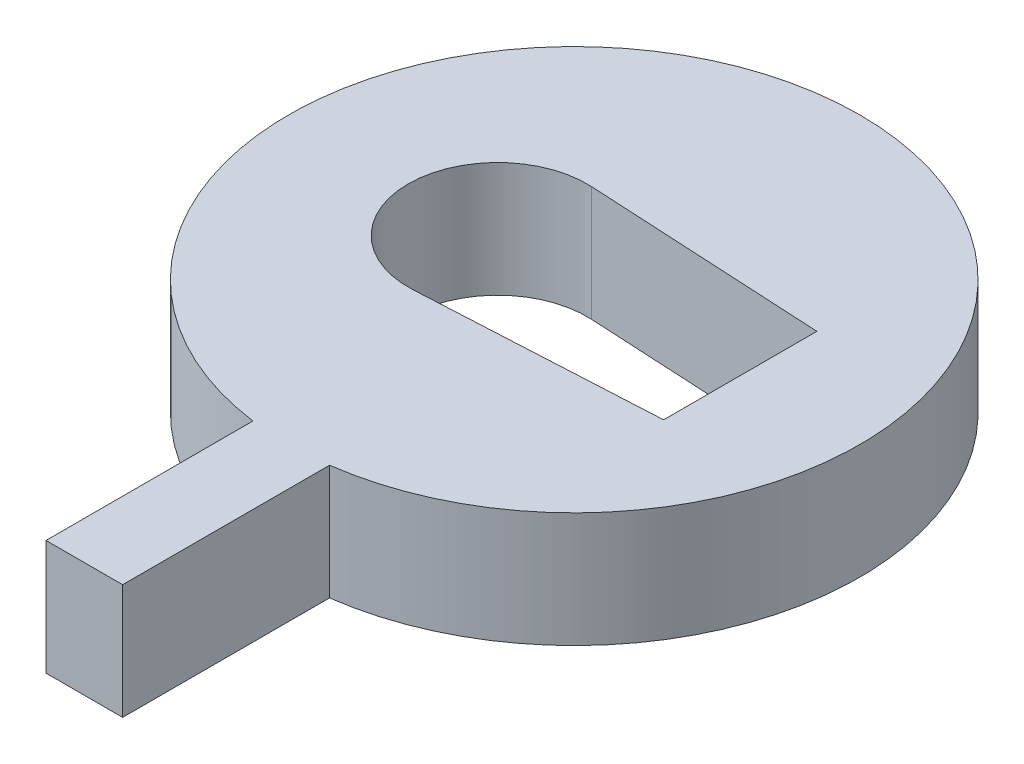
SolidWorks part; units mm, degrees
ref_plane "前视基准面" through (0, 0, 0) normal (0, 0, 1) x (1, 0, 0)
ref_plane "上视基准面" through (0, 0, 0) normal (0, 1, 0) x (1, 0, 0)
ref_plane "右视基准面" through (0, 0, 0) normal (1, 0, 0) x (0, 0, -1)
other "Configuration Table"
sketch "草图1" plane through (0, 0, 0) normal (0, 1, 0) x (1, 0, 0)
  line L1 (10, -5) -> (-10, -5)
  line L2 (10, -5) -> (10, 5)
  line L3 (10, 5) -> (-10, 5)
  line L4 (-10, -5) -> (-10, 5)
  line L5 (10, -5) -> (-10, 5) construction
  line L6 (10, 5) -> (-10, -5) construction
  point P0 (0, 0)
  dimension "D1" = 20
  dimension "D2" = 10
extrude "凸台-拉伸1" add sketch "草图1" along normal blind 4.5
sketch "草图2" plane through (0, 4.5, 0) normal (0, 1, 0) x (1, 0, 0)
  line L0 (-2.8142, 3.4951) -> (6.5, 3)
  line L1 (6.5, 3) -> (6.5, -3)
  line L2 (6.5, -3) -> (-2.8142, -3.4951)
  line L3 (0, 5) -> (0, -5) construction
  line L4 (-6.5, 0) -> (6.5, 0) construction
  line L5 (10, 5) -> (-10, 5) construction
  line L6 (-10, -5) -> (10, -5) construction
  arc A1 (-2.8142, 3.4951) -> (-2.8142, -3.4951) centre (-3, 0) ccw
  point P4 (6.5, 0)
  point P8 (0, 0)
  dimension "D2" = 6
  dimension "D3" = 9.5
extrude "切除-拉伸1" cut sketch "草图2" against normal up to surface (4.5 mm away) contours L2 A1 L0 L1 up to face at (0, 0, 0)
sketch "草图3" plane through (0, 4.5, 0) normal (0, 1, 0) x (1, 0, 0)
  line L4 (-10, 5) -> (-10, -5)
  line L5 (-10, -5) -> (10, -5)
  line L6 (10, -5) -> (10, 5)
  line L7 (10, 5) -> (-10, 5)
  line L8 (-10, 5) -> (-10, -5)
  line L9 (-10, -5) -> (10, -5)
  line L10 (10, -5) -> (10, 5)
  line L11 (10, 5) -> (-10, 5)
  circle A0 centre (0, 0) radius 11.1803
  line M5 (-10, 5) -> (-10, -5)
  line M6 (-10, -5) -> (10, -5)
  line M7 (10, -5) -> (10, 5)
  line M8 (10, 5) -> (-10, 5)
  dimension "D1" = 0
extrude "凸台-拉伸2" add sketch "草图3" against normal up to surface (4.5 mm away) contours A0 M8 | A0 M5 | A0 M6 | A0 M7 up to face at (0, 0, 0)
sketch "草图5" plane through (0, 4.5, 0) normal (0, 1, 0) x (1, 0, 0)
  line L0 (0, 0) -> (0, -8.5253) construction
  line L1 (1.5, -11.1803) -> (-1.5, -11.1803)
  line L2 (1.5, -11.1803) -> (1.5, -8.1803)
  line L3 (1.5, -8.1803) -> (-1.5, -8.1803)
  line L4 (-1.5, -11.1803) -> (-1.5, -8.1803)
  line L5 (1.5, -11.1803) -> (-1.5, -8.1803) construction
  line L6 (1.5, -8.1803) -> (-1.5, -11.1803) construction
  circle A0 centre (0, 0) radius 11.1803 construction
  point P0 (0, -9.6803)
  point P8 (0, 0)
  dimension "D1" = 3
  dimension "D2" = 3
extrude "切除-拉伸2" cut sketch "草图5" against normal up to surface (4.5 mm away) contours L2 L1 L4 L3 up to face at (0, 0, 11.1803)
sketch "草图6" plane through (0, 0, 8.1803) normal (0, 0, 1) x (1, 0, 0)
  line L4 (-1.5, 0) -> (1.5, 0)
  line L5 (1.5, 0) -> (1.5, 4.5)
  line L6 (1.5, 4.5) -> (-1.5, 4.5)
  line L7 (-1.5, 4.5) -> (-1.5, 0)
  line L8 (-1.5, 0) -> (1.5, 0)
  line L9 (1.5, 0) -> (1.5, 4.5)
  line L10 (1.5, 4.5) -> (-1.5, 4.5)
  line L11 (-1.5, 4.5) -> (-1.5, 0)
  dimension "D1" = 0
extrude "凸台-拉伸3" add sketch "草图6" along normal blind 11 contours L8 L9 L10 L11
